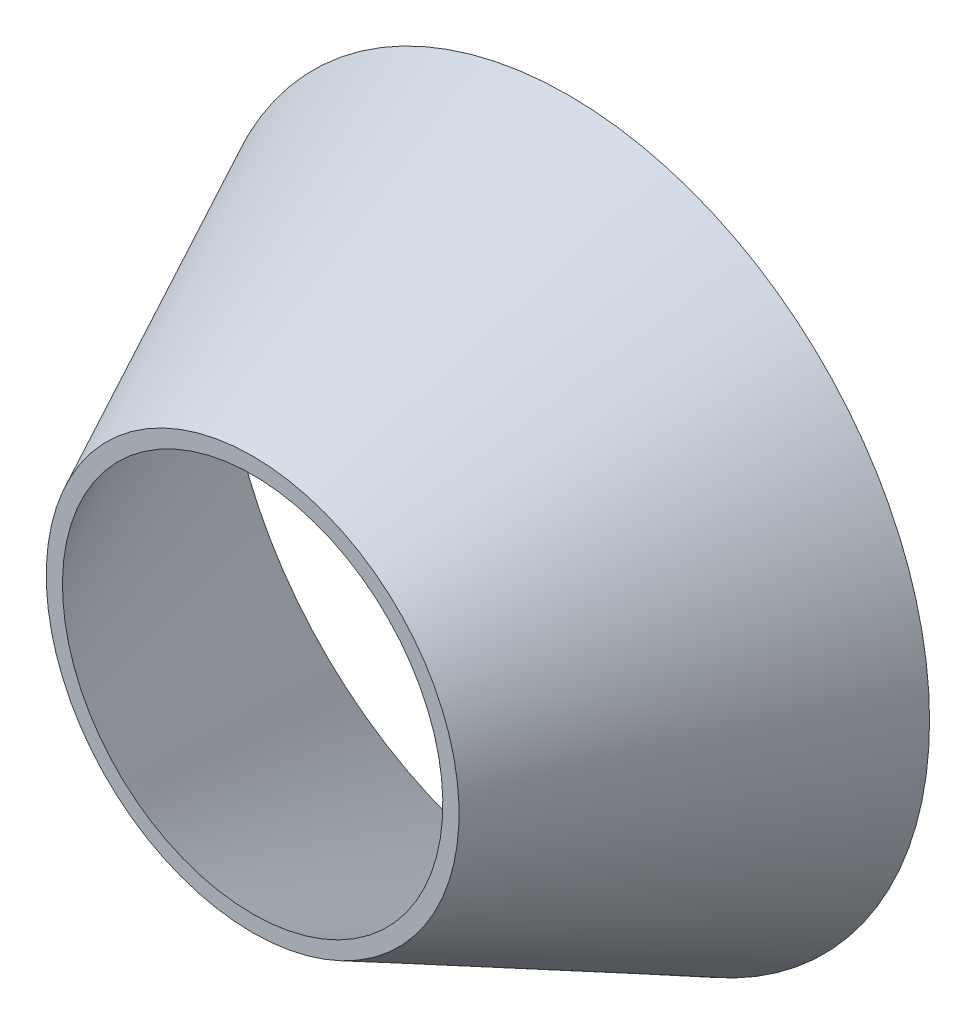
SolidWorks part; units mm, degrees
ref_plane "Front Plane" through (0, 0, 0) normal (0, 0, 1) x (1, 0, 0)
ref_plane "Top Plane" through (0, 0, 0) normal (0, 1, 0) x (1, 0, 0)
ref_plane "Right Plane" through (0, 0, 0) normal (1, 0, 0) x (0, 0, -1)
sketch "Sketch1" plane through (0, 0, 0) normal (1, 0, 0) x (0, 0, -1)
  line L0 (2326.3891, 495.7952) -> (2326.3891, 473.529)
  line L2 (1892.5171, 283.4797) -> (2326.3891, 495.7952)
  line L5 (1892.5171, 261.2135) -> (2326.3891, 473.529)
  line L6 (1892.5171, 283.4797) -> (1892.5171, 261.2135)
  line L8 (1748.8336, 213.1681) -> (2326.3891, 495.7952) construction
  line L9 (1757.6245, 195.2037) -> (2335.18, 477.8308) construction
  line L10 (1891.0777, 0) -> (2326.3891, 0) construction
  dimension "D2" = 283.4797
  dimension "D3" = 495.7952
  dimension "D4" = 433.8721
  dimension "D1" = 20
revolve "Revolve1" add sketch "Sketch1" angle 360 about L10
sketch "Sketch2" plane through (0, 0, 0) normal (0, 1, 0) x (1, 0, 0)
  line L0 (0, 1892.5171) -> (0, 2326.3891) construction
  line L1 (-283.4797, 1892.5171) -> (283.4797, 1892.5171) construction
  line L2 (473.529, 2326.3891) -> (-473.529, 2326.3891) construction
